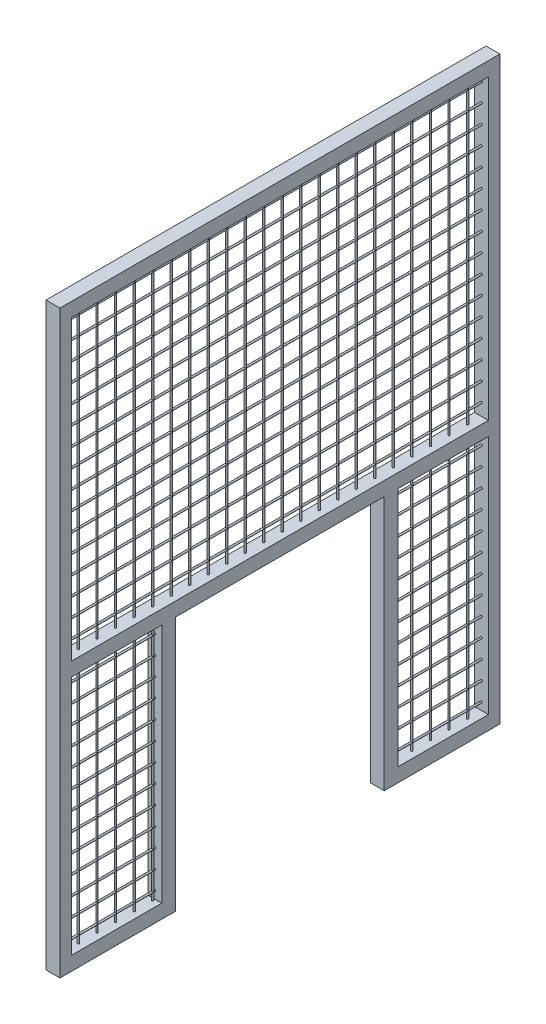
SolidWorks part; units mm, degrees
ref_plane "Piano frontale" through (0, 0, 0) normal (0, 0, 1) x (1, 0, 0)
ref_plane "Piano superiore" through (0, 0, 0) normal (0, 1, 0) x (1, 0, 0)
ref_plane "Piano destro" through (0, 0, 0) normal (1, 0, 0) x (0, 0, -1)
sketch "Schizzo1" plane through (0, 0, 1950) normal (0, 0, -1) x (-1, 0, 0)
  line L0 (-50, 2555) -> (-50, 50) construction
  line L1 (-30, 110) -> (30, 110)
  line L2 (-30, 110) -> (-30, 50)
  line L3 (-30, 50) -> (30, 50)
  line L4 (30, 110) -> (30, 50)
  line L5 (50, 2555) -> (50, 50) construction
  line L6 (-100, 50) -> (100, 50) construction
  line L7 (50, 2555) -> (-50, 2555) construction
  line L8 (-30, 2555) -> (30, 2555)
  line L9 (-30, 2555) -> (-30, 2495)
  line L10 (-30, 2495) -> (30, 2495)
  line L11 (30, 2555) -> (30, 2495)
  circle A0 centre (0, 2462.5) radius 3.75
  circle A1 centre (0, 2382.5) radius 3.75
  circle A2 centre (0, 2302.5) radius 3.75
  circle A3 centre (0, 2222.5) radius 3.75
  circle A4 centre (0, 2142.5) radius 3.75
  circle A5 centre (0, 2062.5) radius 3.75
  circle A6 centre (0, 1982.5) radius 3.75
  circle A7 centre (0, 1902.5) radius 3.75
  circle A8 centre (0, 1822.5) radius 3.75
  circle A9 centre (0, 1742.5) radius 3.75
  circle A10 centre (0, 1662.5) radius 3.75
  circle A11 centre (0, 1582.5) radius 3.75
  circle A12 centre (0, 1502.5) radius 3.75
  circle A13 centre (0, 1422.5) radius 3.75
  circle A14 centre (0, 1342.5) radius 3.75
  circle A15 centre (0, 1262.5) radius 3.75
  circle A16 centre (0, 1182.5) radius 3.75
  circle A17 centre (0, 1102.5) radius 3.75
  circle A18 centre (0, 1022.5) radius 3.75
  circle A19 centre (0, 942.5) radius 3.75
  circle A20 centre (0, 862.5) radius 3.75
  circle A21 centre (0, 782.5) radius 3.75
  circle A22 centre (0, 702.5) radius 3.75
  circle A23 centre (0, 622.5) radius 3.75
  circle A24 centre (0, 542.5) radius 3.75
  circle A25 centre (0, 462.5) radius 3.75
  circle A26 centre (0, 382.5) radius 3.75
  circle A27 centre (0, 302.5) radius 3.75
  circle A28 centre (0, 222.5) radius 3.75
  circle A29 centre (0, 142.5) radius 3.75
  dimension "D8" = 7.5
  dimension "D1" = 20
  dimension "D2" = 20
  dimension "D3" = 0
  dimension "D4" = 60
  dimension "D5" = 60
  dimension "D6" = 20
  dimension "D7" = 60
  dimension "D10" = 32.5
  dimension "D9" = 30
extrude "Estrusione-Estrusione1" add sketch "Schizzo1" along normal up to surface (1900 mm away)
sketch "Schizzo2" plane through (0, 110, 0) normal (0, 1, 0) x (1, 0, 0)
  line L0 (100, -100) -> (-100, -100) construction
  line L1 (-30, -50) -> (30, -50)
  line L2 (-30, -50) -> (-30, -100)
  line L3 (-30, -100) -> (30, -100)
  line L4 (30, -50) -> (30, -100)
  line L5 (30, -50) -> (30, -1950) construction
  line L16 (-30, -50) -> (-30, -1950) construction
  line L17 (-30, -1950) -> (30, -1950)
  line L18 (-30, -1950) -> (-30, -1900)
  line L19 (-30, -1900) -> (30, -1900)
  line L20 (30, -1950) -> (30, -1900)
  line L22 (-30, -1950) -> (30, -1950) construction
  circle A0 centre (0, -160) radius 3.75
  circle A22 centre (0, -240) radius 3.75
  circle A23 centre (0, -320) radius 3.75
  circle A24 centre (0, -400) radius 3.75
  circle A25 centre (0, -480) radius 3.75
  circle A26 centre (0, -560) radius 3.75
  circle A27 centre (0, -640) radius 3.75
  circle A28 centre (0, -720) radius 3.75
  circle A31 centre (0, -800) radius 3.75
  circle A32 centre (0, -880) radius 3.75
  circle A33 centre (0, -960) radius 3.75
  circle A34 centre (0, -1040) radius 3.75
  circle A35 centre (0, -1120) radius 3.75
  circle A36 centre (0, -1200) radius 3.75
  circle A37 centre (0, -1280) radius 3.75
  circle A38 centre (0, -1360) radius 3.75
  circle A39 centre (0, -1440) radius 3.75
  circle A40 centre (0, -1520) radius 3.75
  circle A41 centre (0, -1600) radius 3.75
  circle A42 centre (0, -1680) radius 3.75
  circle A43 centre (0, -1760) radius 3.75
  circle A44 centre (0, -1840) radius 3.75
  dimension "D3" = 60
  dimension "D5" = 7.5
  dimension "D1" = 50
  dimension "D2" = 60
  dimension "D8" = 0
extrude "Estrusione-Estrusione2" add sketch "Schizzo2" along normal up to surface (2385 mm away) up to face at (0, 2495, 1000)
sketch "Schizzo3" plane through (30, 0, 0) normal (1, 0, 0) x (0, 0, -1)
  line L0 (-50, 50) -> (-1950, 50) construction
  line L1 (-1450, 50) -> (-550, 50)
  line L2 (-1450, 50) -> (-1450, 1150)
  line L3 (-1450, 1150) -> (-550, 1150)
  line L4 (-550, 50) -> (-550, 1150)
  line L5 (-1950, 2555) -> (-1950, 50) construction
  line L6 (-50, 2555) -> (-50, 50) construction
  dimension "D1" = 500
  dimension "D2" = 500
  dimension "D3" = 1100
extrude "Taglio-Estrusione1" cut sketch "Schizzo3" against normal blind 279
sketch "Schizzo4" plane through (0, 110, 0) normal (0, 1, 0) x (1, 0, 0)
  line L1 (30, -1450) -> (-30, -1450)
  line L2 (30, -1450) -> (30, -1510)
  line L3 (30, -1510) -> (-30, -1510)
  line L4 (-30, -1450) -> (-30, -1510)
  line L5 (30, -550) -> (-30, -550)
  line L6 (30, -550) -> (30, -490)
  line L7 (30, -490) -> (-30, -490)
  line L8 (-30, -550) -> (-30, -490)
extrude "Estrusione-Estrusione3" add sketch "Schizzo4" along normal blind 1100
sketch "Schizzo5" plane through (0, 0, 1450) normal (0, 0, -1) x (-1, 0, 0)
  line L1 (-30, 1210) -> (30, 1210)
  line L2 (-30, 1210) -> (-30, 1150)
  line L3 (-30, 1150) -> (30, 1150)
  line L4 (30, 1210) -> (30, 1150)
extrude "Estrusione-Estrusione4" add sketch "Schizzo5" along normal up to surface and the other way up to next
